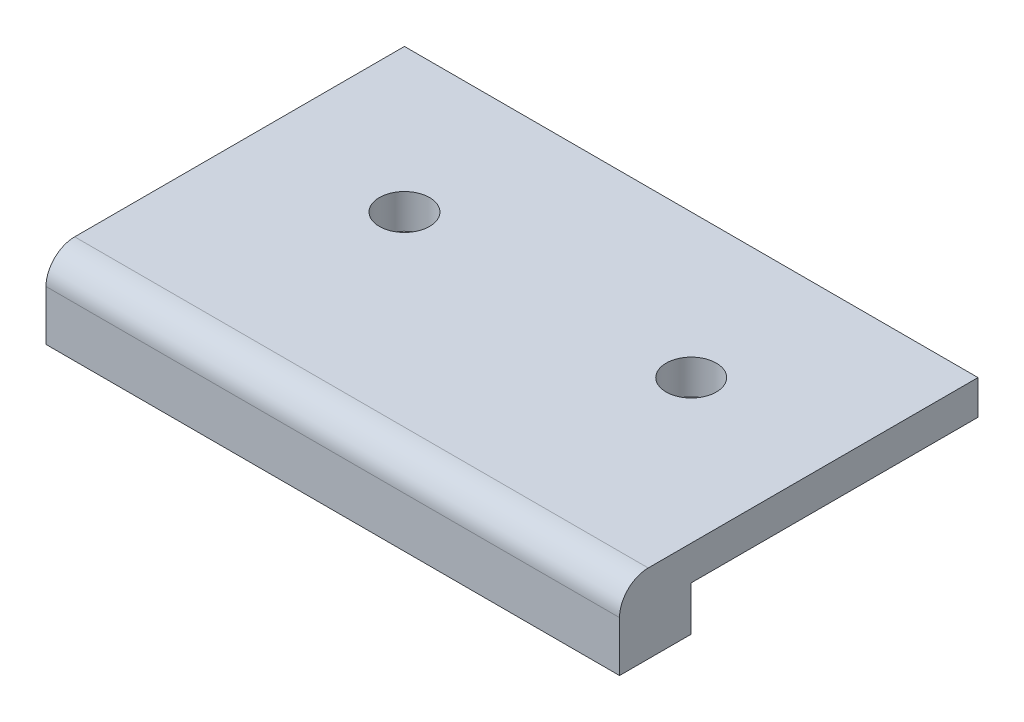
SolidWorks part; units mm, degrees
ref_plane "Front Plane" through (0, 0, 0) normal (0, 0, 1) x (1, 0, 0)
ref_plane "Top Plane" through (0, 0, 0) normal (0, 1, 0) x (1, 0, 0)
ref_plane "Right Plane" through (0, 0, 0) normal (1, 0, 0) x (0, 0, -1)
sketch "Sketch1" plane through (0, 0, 0) normal (0, 1, 0) x (1, 0, 0)
  line L0 (0, 10) -> (40, 10) construction
  line L1 (0, 0) -> (40, 0)
  line L2 (0, 0) -> (0, 20)
  line L3 (0, 20) -> (40, 20)
  line L4 (40, 0) -> (40, 20)
  line L5 (20, 20) -> (20, 0) construction
  circle A0 centre (10, 10) radius 1.75
  circle A1 centre (30, 10) radius 1.75
  dimension "D3" = 3.5
  dimension "D4" = 10
  dimension "D1" = 20
  dimension "D2" = 40
extrude "Boss-Extrude1" add sketch "Sketch1" along normal blind 2.4
sketch "Sketch2" plane through (0, 2.4, 0) normal (0, 1, 0) x (1, 0, 0)
  line L0 (40, 0) -> (40, -5) construction
  line L6 (0, 0) -> (40, 0)
  line L7 (0, 0) -> (0, -5)
  line L8 (0, -5) -> (40, -5)
  line L9 (40, 0) -> (40, -5)
  dimension "D1" = 5
extrude "Boss-Extrude2" add sketch "Sketch2" against normal blind 5.5
fillet "Fillet1" radius 2 1 edges at (20, 2.4, 5)
